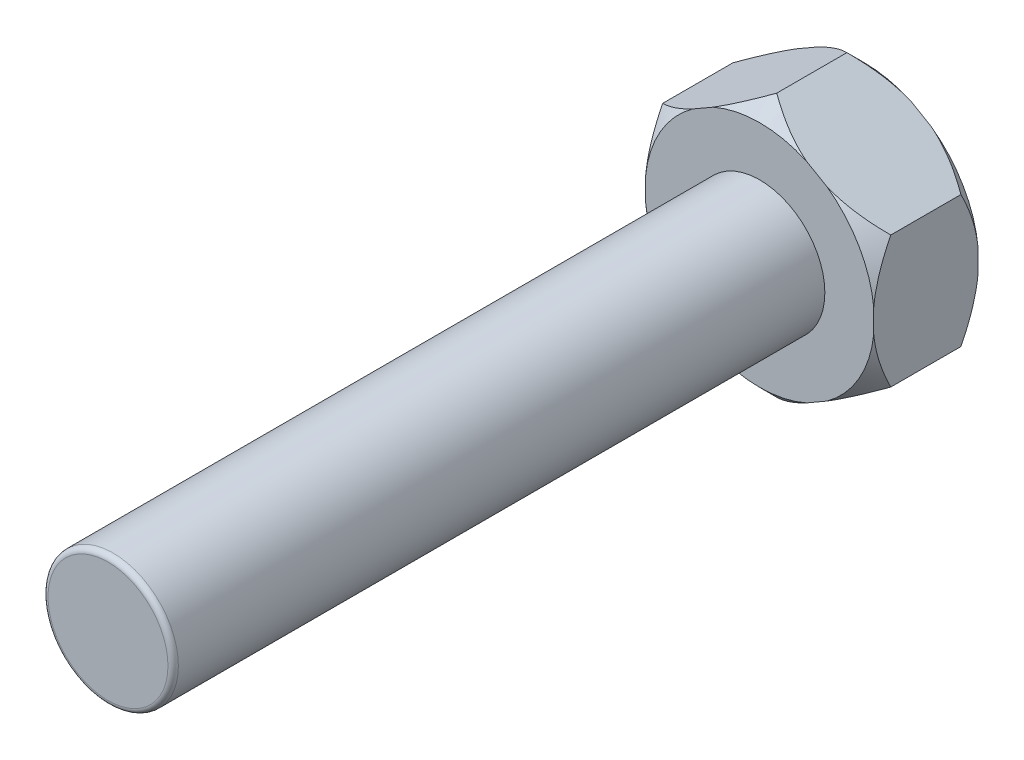
SolidWorks part; units mm, degrees
ref_plane "前视基准面" through (0, 0, 0) normal (0, 0, 1) x (1, 0, 0)
ref_plane "上视基准面" through (0, 0, 0) normal (0, 1, 0) x (1, 0, 0)
ref_plane "右视基准面" through (0, 0, 0) normal (1, 0, 0) x (0, 0, -1)
sketch "草图1" plane through (0, 0, 0) normal (0, 0, 1) x (1, 0, 0)
  line L1 (0, 4.0415) -> (-3.5, 2.0207)
  line L2 (-3.5, 2.0207) -> (-3.5, -2.0207)
  line L3 (-3.5, -2.0207) -> (0, -4.0415)
  line L4 (0, -4.0415) -> (3.5, -2.0207)
  line L5 (3.5, -2.0207) -> (3.5, 2.0207)
  line L6 (3.5, 2.0207) -> (0, 4.0415)
  circle A0 centre (0, 0) radius 3.5 construction
  dimension "D1" = 7
extrude "凸台-拉伸1" add sketch "草图1" against normal blind 3.2
sketch "草图2" plane through (0, 0, 0) normal (0, 0, 1) x (1, 0, 0)
  circle A0 centre (0, 0) radius 2
  dimension "D1" = 4
extrude "凸台-拉伸2" add sketch "草图2" along normal blind 20
fillet "圆角1" radius 0.16 1 edges at (2, 0, 20)
sketch "草图3" plane through (0, 0, 0) normal (1, 0, 0) x (0, 0, -1)
  line L0 (0, 0) -> (-7.5807, 0) construction
  line L1 (0.523, 4.0415) -> (0, 3.5185)
  line L2 (3.2, 4.0415) -> (0, 4.0415) construction
  line L3 (0, 2.0207) -> (0, 4.0415) construction
  line L4 (0, 3.5185) -> (0, 4.0415)
  line L5 (0, 4.0415) -> (0.523, 4.0415)
  line L6 (3.2, 4.0415) -> (3.2, 3.5185)
  line L7 (3.2, 2.0207) -> (3.2, 4.0415) construction
  line L8 (3.2, 3.5185) -> (2.677, 4.0415)
  line L9 (2.677, 4.0415) -> (3.2, 4.0415)
  point P16 (0.5519, 4.0415)
revolve "切除-旋转1" cut sketch "草图3" angle 360 about L0
